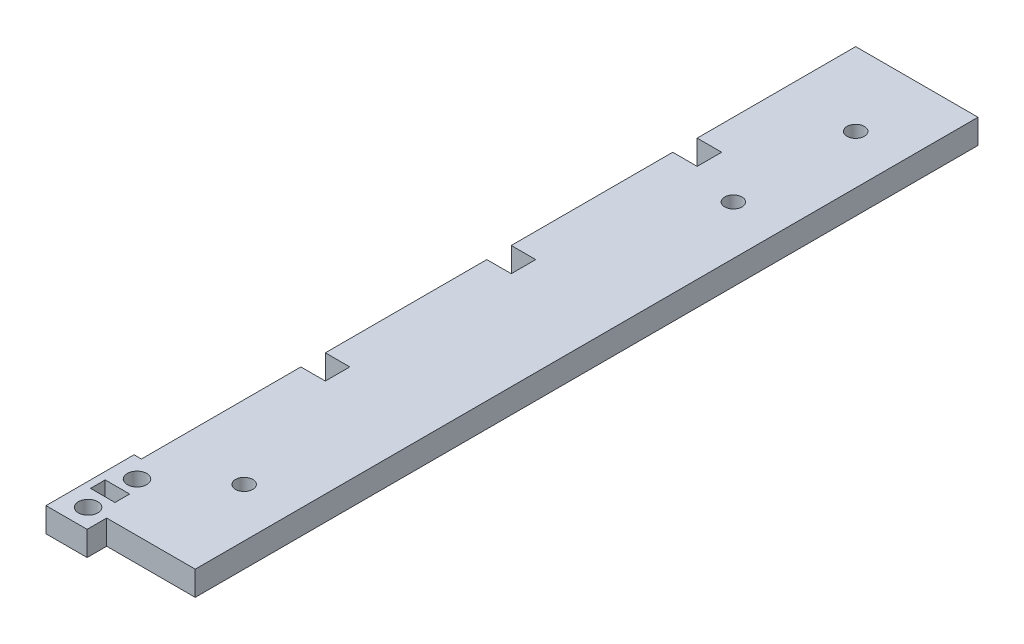
SolidWorks part; units mm, degrees
ref_plane "Front Plane" through (0, 0, 0) normal (0, 0, 1) x (1, 0, 0)
ref_plane "Top Plane" through (0, 0, 0) normal (0, 1, 0) x (1, 0, 0)
ref_plane "Right Plane" through (0, 0, 0) normal (1, 0, 0) x (0, 0, -1)
sketch "Sketch1" plane through (0, 0, 0) normal (0, 1, 0) x (1, 0, 0)
  line L8 (8.763, -10.3314) -> (8.763, -15.4114)
  line L11 (0, 192.8686) -> (31.75, 192.8686)
  line L12 (31.75, -10.3314) -> (31.75, 192.8686)
  line L13 (8.763, -15.4114) -> (-1.905, -15.4114)
  line L14 (-1.905, -15.4114) -> (-1.905, 7.4486)
  line L15 (-1.905, 7.4486) -> (0, 7.4486)
  line L16 (8.763, -10.3314) -> (31.75, -10.3314)
  line L17 (0, 7.4486) -> (0, 192.8686)
  dimension "D1" = 31.75
  dimension "D2" = 203.2
  dimension "D3" = 1.905
  dimension "D4" = 22.86
  dimension "D5" = 8.763
  dimension "D6" = 5.08
extrude "Boss-Extrude1" add sketch "Sketch1" along normal blind 6.35
sketch "Sketch2" plane through (0, 6.35, 0) normal (0, 1, 0) x (1, 0, 0)
  line L0 (0, 192.8686) -> (0, 7.4486) construction
  line L1 (0, 55.2006) -> (6.35, 55.2006)
  line L2 (0, 55.2006) -> (0, 48.8506)
  line L3 (0, 48.8506) -> (6.35, 48.8506)
  line L4 (6.35, 55.2006) -> (6.35, 48.8506)
  line L6 (0, 103.4606) -> (6.35, 103.4606)
  line L7 (0, 103.4606) -> (0, 97.1106)
  line L8 (0, 97.1106) -> (6.35, 97.1106)
  line L9 (6.35, 103.4606) -> (6.35, 97.1106)
  line L10 (0, 151.7206) -> (6.35, 151.7206)
  line L11 (0, 151.7206) -> (0, 145.3706)
  line L12 (0, 145.3706) -> (6.35, 145.3706)
  line L13 (6.35, 151.7206) -> (6.35, 145.3706)
  line L15 (8.763, -10.3314) -> (31.75, -10.3314) construction
  dimension "D1" = 6.35
  dimension "D2" = 6.35
  dimension "D3" = 6.35
  dimension "D4" = 6.35
  dimension "D5" = 59.182
  dimension "D6" = 6.35
  dimension "D7" = 6.35
  dimension "D8" = 41.91
  dimension "D9" = 41.91
extrude "Cut-Extrude1" cut sketch "Sketch2" against normal through all
hole_wizard "#8 (0.199) Diameter Hole1" positions "Sketch3" profile "Sketch4" hole size "#8" standard "ANSI Inch" end condition through all
sketch "Sketch3" plane through (0, 6.35, 0) normal (0, 1, 0) x (1, 0, 0)
  line L0 (-1.905, 7.4486) -> (-1.905, -15.4114) construction
  line L1 (0, 7.4486) -> (-1.905, 7.4486) construction
  point P0 (3.937, 2.3686)
  point P2 (3.937, -10.3314)
  dimension "D1" = 5.842
  dimension "D2" = 5.08
  dimension "D3" = 12.7
sketch "Sketch4" plane through (3.937, 6.35, -2.3686) normal (1, 0, 0) x (0, 0, 1)
  line L0 (0, 0) -> (0, 6.35)
  line L1 (0, 6.35) -> (2.5273, 6.35)
  line L2 (2.5273, 6.35) -> (2.5273, 0)
  line L5 (2.5273, 0) -> (0, 0)
  line L11 (0, -6.35) -> (0, 107.95) construction
  dimension "Thru Hole Dia." = 5.0546
  dimension "Thru Hole Depth" = 6.35
sketch "Sketch5" plane through (0, 6.35, 0) normal (0, 1, 0) x (1, 0, 0)
  line L0 (0, 7.4486) -> (0, -15.4114) construction
  line L1 (-1.905, -15.4114) -> (8.763, -15.4114) construction
  line L2 (0, -1.9494) -> (6.35, -1.9494)
  line L3 (6.35, -1.9494) -> (6.35, -5.7594)
  line L4 (6.35, -5.7594) -> (0, -5.7594)
  line L5 (8.763, -10.3314) -> (31.75, -10.3314) construction
  line L6 (0, -5.7594) -> (0, -1.9494)
  dimension "D1" = 4.572
  dimension "D2" = 6.35
  dimension "D3" = 3.81
extrude "Cut-Extrude2" cut sketch "Sketch5" against normal through all
hole_wizard "CBORE for #8 Binding Head Machine Screw1" positions "Sketch8" profile "Sketch9" counterbore size "#8" standard "ANSI Inch" end condition through all
sketch "Sketch8" plane through (0, 0, 0) normal (0, -1, 0) x (-1, 0, 0)
  line L0 (-31.75, -10.3314) -> (-31.75, 192.8686) construction
  line L1 (-31.75, 192.8686) -> (0, 192.8686) construction
  point P0 (-19.05, 173.8186)
  point P2 (-19.05, 142.0686)
  point P4 (-19.05, 15.0686)
  dimension "D1" = 12.7
  dimension "D2" = 19.05
  dimension "D3" = 50.8
  dimension "D4" = 177.8
sketch "Sketch9" plane through (19.05, 0, -173.8186) normal (1, 0, 0) x (0, 0, -1)
  line L0 (0, 0) -> (0, 6.35)
  line L1 (0, 6.35) -> (2.2479, 6.35)
  line L3 (2.2479, 6.35) -> (2.2479, 3.175)
  line L4 (2.2479, 3.175) -> (4.7625, 3.175)
  line L5 (4.7625, 3.175) -> (4.7625, 0)
  line L7 (4.7625, 0) -> (0, 0)
  line L11 (0, -6.35) -> (0, 107.95) construction
  dimension "Thru Hole Dia." = 4.4958
  dimension "Thru Hole Depth" = 6.35
  dimension "C'Bore Dia." = 9.525
  dimension "C'Bore Depth" = 3.175
